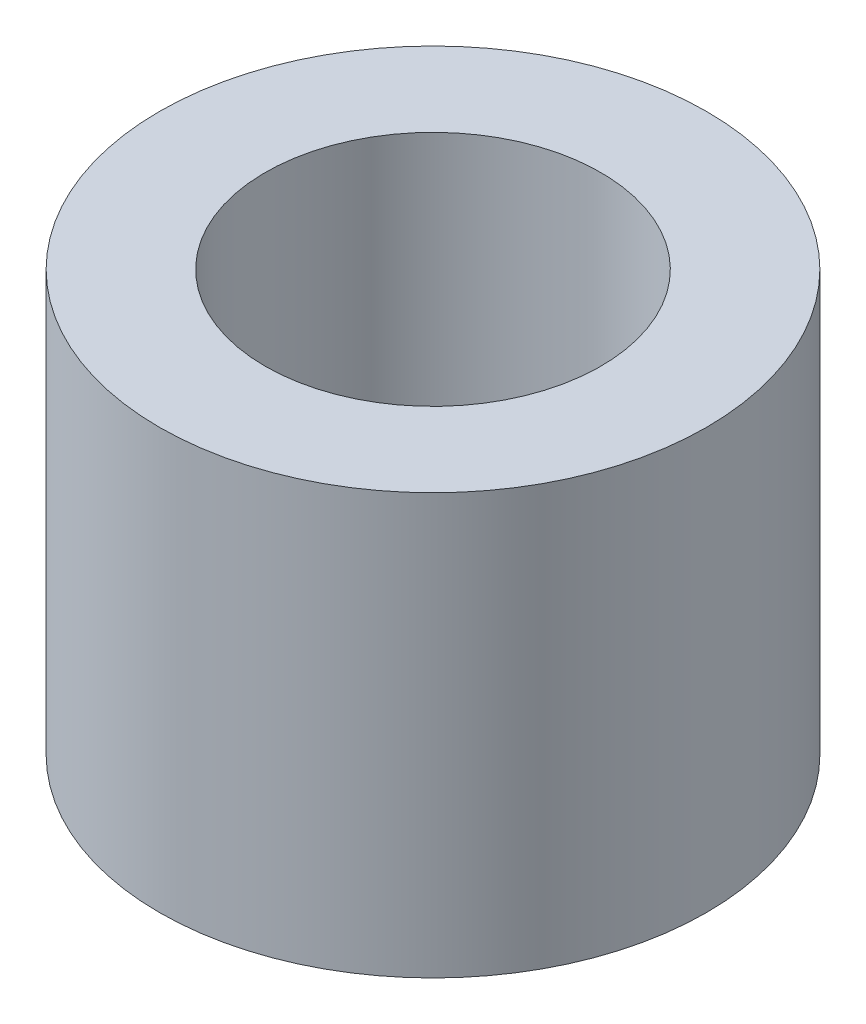
SolidWorks part; units mm, degrees
ref_plane "Front Plane" through (0, 0, 0) normal (0, 0, 1) x (1, 0, 0)
ref_plane "Top Plane" through (0, 0, 0) normal (0, 1, 0) x (1, 0, 0)
ref_plane "Right Plane" through (0, 0, 0) normal (1, 0, 0) x (0, 0, -1)
sketch "Sketch1" plane through (0, 0, 0) normal (0, 1, 0) x (1, 0, 0)
  circle A0 centre (0, 0) radius 5.1752
  circle A1 centre (0, 0) radius 3.175
  dimension "D1" = 10.3505
  dimension "D2" = 6.35
extrude "Boss-Extrude1" add sketch "Sketch1" along normal blind 7.9502
